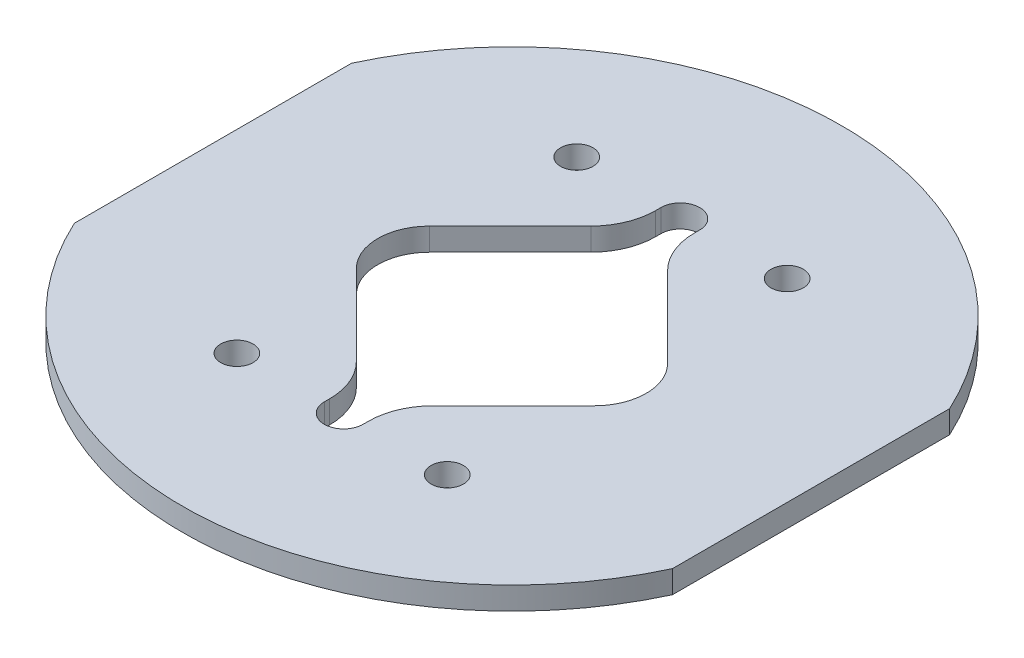
SolidWorks part; units mm, degrees
material "Silicon"
ref_plane "Front Plane" through (0, 0, 0) normal (0, 0, 1) x (1, 0, 0)
ref_plane "Top Plane" through (0, 0, 0) normal (0, 1, 0) x (1, 0, 0)
ref_plane "Right Plane" through (0, 0, 0) normal (1, 0, 0) x (0, 0, -1)
sketch "Sketch1" plane through (0, 0, 0) normal (0, 1, 0) x (1, 0, 0)
  line L2 (-23.1, 0) -> (23.1, 0) construction
  line L3 (-23.1, -10.7052) -> (-23.1, 10.7052)
  line L4 (23.1, 10.7052) -> (23.1, -10.7052)
  arc A1 (23.1, -10.7052) -> (-23.1, -10.7052) centre (0, 0) cw
  arc A2 (-23.1, 10.7052) -> (23.1, 10.7052) centre (0, 0) cw
  point P7 (0, 0)
  point P10 (23.1, 0)
  dimension "D1" = 25.46
  dimension "D2" = 46.2
extrude "Boss-Extrude1" add sketch "Sketch1" along normal blind 1.75
sketch "Sketch3" plane through (0, 1.75, 0) normal (0, 1, 0) x (1, 0, 0)
  line L0 (0, -12.0208) -> (-12.0208, 0)
  line L1 (0, -12.0208) -> (12.0208, 0)
  line L2 (-12.0208, 0) -> (0, 12.0208)
  line L3 (12.0208, 0) -> (0, 12.0208)
  line L4 (0, -12.0208) -> (0, 12.0208) construction
  line L5 (-12.0208, 0) -> (12.0208, 0) construction
  line L6 (0, 0) -> (0, 25.46) construction
  arc A0 (23.1, 10.7052) -> (-23.1, 10.7052) centre (0, 0) ccw construction
  point P1 (0, 0)
  dimension "D1" = 17
extrude "Cut-Extrude1" cut sketch "Sketch3" against normal through all
sketch "Sketch4" plane through (0, 1.75, 0) normal (0, 1, 0) x (1, 0, 0)
  line L0 (0, 13) -> (0, -13) construction
  line L1 (-1.5, 13) -> (1.5, 13) construction
  line L2 (-1.5, 13) -> (-1.5, -13)
  line L6 (1.5, -13) -> (1.5, 13)
  arc A2 (1.5, 13) -> (-1.5, 13) centre (0, 13) ccw
  arc A3 (1.5, -13) -> (-1.5, -13) centre (0, -13) cw
  point P6 (0, 0)
  dimension "D3" = 1.5
  dimension "D2" = 13
extrude "Cut-Extrude2" cut sketch "Sketch4" against normal blind 1.75
fillet "Fillet2" radius 5 4 edges at (1.5, 0.875, -10.5208) (-1.5, 0.875, -10.5208) (-1.5, 0.875, 10.5208) (1.5, 0.875, 10.5208)
fillet "Fillet1" radius 4 2 edges at (12.0208, 0.875, 0) (-12.0208, 0.875, 0)
sketch "Sketch6" plane through (0, 1.75, 0) normal (0, 1, 0) x (1, 0, 0)
  line L0 (-8.125, 13.125) -> (8.125, 13.125) construction
  line L1 (0, 0) -> (0, 13.125) construction
  circle A1 centre (-8.125, 13.125) radius 1.25
  circle A2 centre (8.125, 13.125) radius 1.25
  point P5 (0, 13.125)
  dimension "D3" = 2.5
  dimension "D1" = 13.125
  dimension "D2" = 16.25
extrude "Cut-Extrude3" cut sketch "Sketch6" against normal through all
pattern_circular "CirPattern3" count 2 over 360 about axis through (0, 0, 0) along (0, 1, 0) of "Cut-Extrude3"
